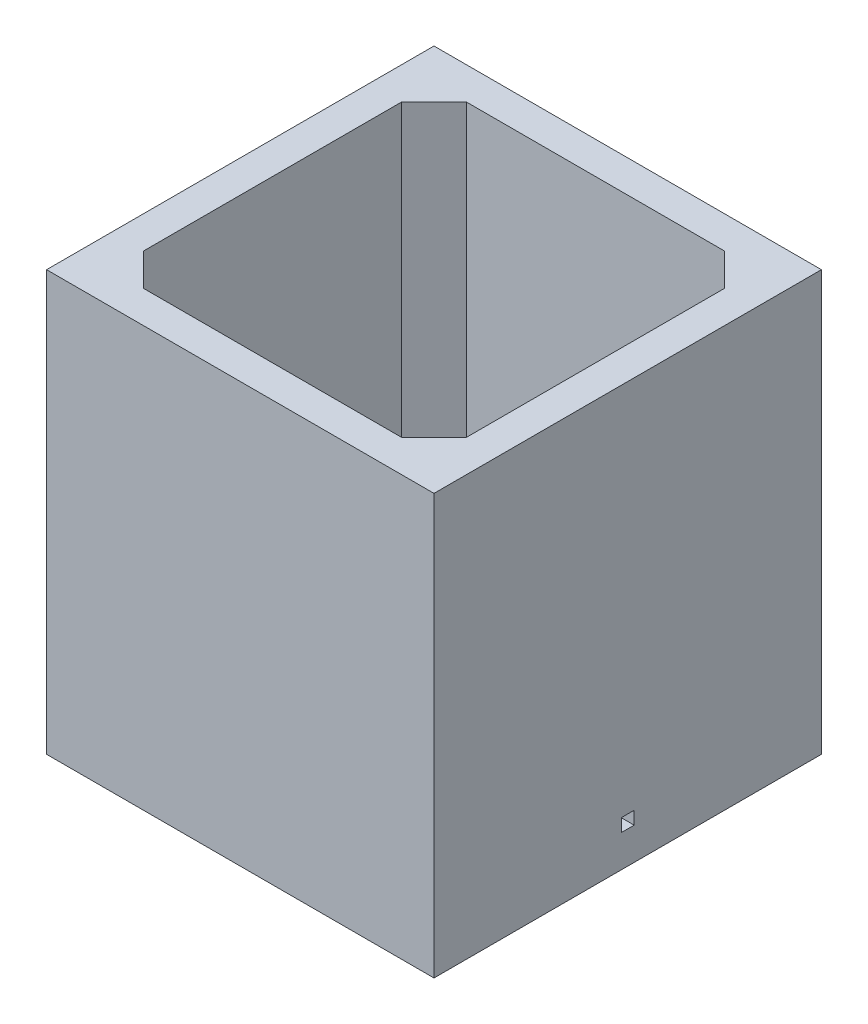
SolidWorks part; units mm, degrees
ref_plane "Front Plane" through (0, 0, 0) normal (0, 0, 1) x (1, 0, 0)
ref_plane "Top Plane" through (0, 0, 0) normal (0, 1, 0) x (1, 0, 0)
ref_plane "Right Plane" through (0, 0, 0) normal (1, 0, 0) x (0, 0, -1)
sketch "Sketch1" plane through (0, 0, 0) normal (0, 1, 0) x (1, 0, 0)
  line L1 (-30, -30) -> (30, -30)
  line L2 (-30, -30) -> (-30, 30)
  line L3 (-30, 30) -> (30, 30)
  line L4 (30, -30) -> (30, 30)
  line L5 (-30, -30) -> (30, 30) construction
  line L6 (-30, 30) -> (30, -30) construction
  line L7 (-25, -25) -> (25, -25)
  line L8 (-25, -25) -> (-25, 25)
  line L9 (-25, 25) -> (25, 25)
  line L10 (25, -25) -> (25, 25)
  line L11 (-25, -25) -> (25, 25) construction
  line L12 (-25, 25) -> (25, -25) construction
  point P0 (0, 0)
  point P6 (0, 0)
  dimension "D1" = 60
  dimension "D2" = 60
  dimension "D3" = 50
  dimension "D4" = 50
extrude "Boss-Extrude1" add sketch "Sketch1" along normal blind 60
sketch "Sketch2" plane through (0, 0, 0) normal (0, -1, 0) x (1, 0, 0)
  line L1 (-30, -30) -> (30, -30)
  line L2 (-30, -30) -> (-30, 30)
  line L3 (-30, 30) -> (30, 30)
  line L4 (30, -30) -> (30, 30)
  line L5 (-30, -30) -> (30, 30) construction
  line L6 (-30, 30) -> (30, -30) construction
  point P0 (0, 0)
extrude "Boss-Extrude2" add sketch "Sketch2" along normal blind 5
sketch "Sketch3" plane through (0, 0, 0) normal (0, 1, 0) x (1, 0, 0)
  circle A0 centre (0, 0) radius 10
  dimension "D1" = 20
extrude "Cut-Extrude1" cut sketch "Sketch3" against normal through all
chamfer "Chamfer4" distance 5 angle 45 4 edges at (25, 30, 25) (25, 30, -25) (-25, 30, -25) (-25, 30, 25)
sketch "Sketch7" plane through (25, 0, 0) normal (-1, 0, 0) x (0, 0, 1)
  line L0 (20, 0) -> (-20, 0) construction
  line L1 (-1, 0) -> (1, 0)
  line L2 (-1, 0) -> (-1, 2)
  line L3 (-1, 2) -> (1, 2)
  line L4 (1, 0) -> (1, 2)
  dimension "D1" = 2
  dimension "D2" = 2
  dimension "D3" = 1
  dimension "D4" = 0
extrude "Cut-Extrude3" cut sketch "Sketch7" against normal up to surface (5 mm away) up to face at (30, 27.5, 0)
